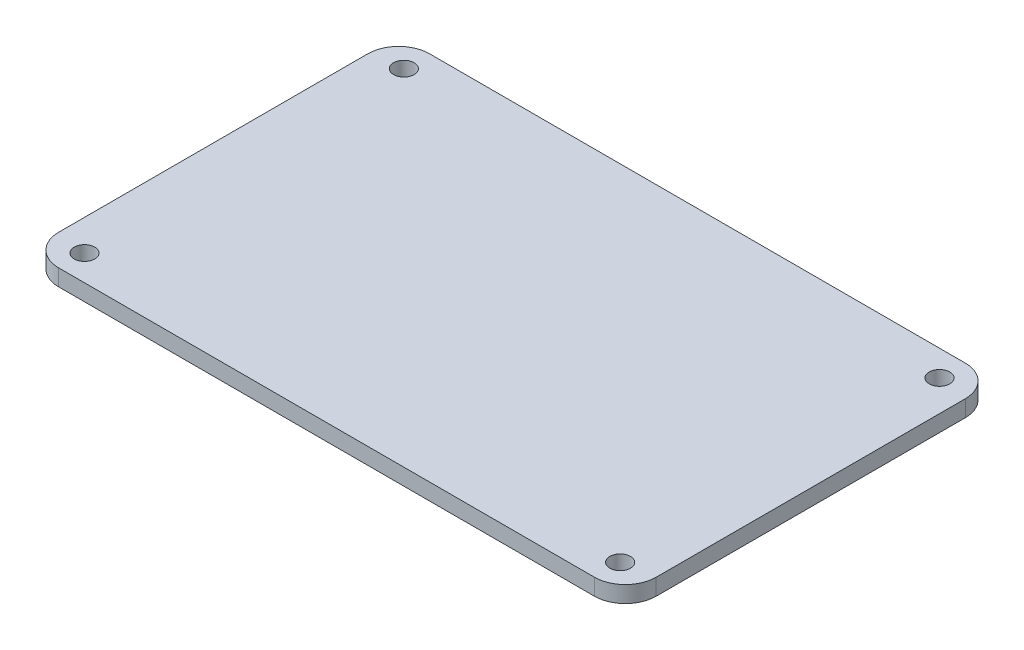
SolidWorks part; units mm, degrees
ref_plane "Front Plane" through (0, 0, 0) normal (0, 0, 1) x (1, 0, 0)
ref_plane "Top Plane" through (0, 0, 0) normal (0, 1, 0) x (1, 0, 0)
ref_plane "Right Plane" through (0, 0, 0) normal (1, 0, 0) x (0, 0, -1)
sketch "Sketch1" plane through (0, 0, 0) normal (0, 1, 0) x (1, 0, 0)
  line L0 (3.0018, 33.5) -> (0, 36) construction
  line L1 (0, 0) -> (58, 0)
  line L2 (0, 0) -> (0, 36)
  line L3 (0, 36) -> (58, 36)
  line L4 (58, 0) -> (58, 36)
  line L5 (3.0018, 33.5) -> (54.9982, 33.5) construction
  line L6 (3.0018, 33.5) -> (3.0018, 2.5) construction
  line L7 (3.0018, 2.5) -> (54.9982, 2.5) construction
  line L8 (54.9982, 33.5) -> (54.9982, 2.5) construction
  line L9 (0, 0) -> (3.0018, 2.5) construction
  line L10 (54.9982, 2.5) -> (58, 0) construction
  line L11 (54.9982, 33.5) -> (58, 36) construction
  circle A0 centre (3.0018, 2.5) radius 1
  circle A1 centre (54.9982, 2.5) radius 1
  circle A2 centre (54.9982, 33.5) radius 1
  circle A3 centre (3.0018, 33.5) radius 1
  dimension "D3" = 2
  dimension "D1" = 58
  dimension "D2" = 36
  dimension "D4" = 2.5
extrude "Boss-Extrude1" add sketch "Sketch1" along normal blind 1.6
fillet "Fillet1" radius 3 4 edges at (0, 0.8, -36) (58, 0.8, -36) (58, 0.8, 0) (0, 0.8, 0)
